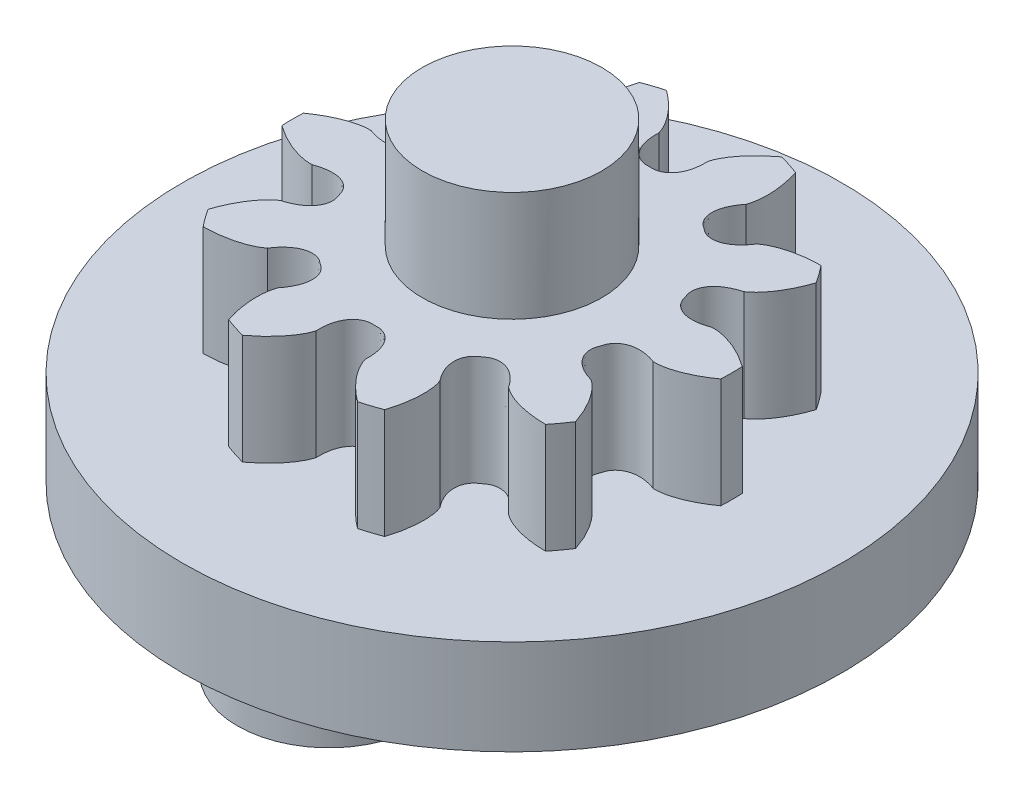
SolidWorks part; units mm, degrees
ref_plane "Front Plane" through (0, 0, 0) normal (0, 0, 1) x (1, 0, 0)
ref_plane "Top Plane" through (0, 0, 0) normal (0, 1, 0) x (1, 0, 0)
ref_plane "Right Plane" through (0, 0, 0) normal (1, 0, 0) x (0, 0, -1)
sketch "Sketch1" plane through (0, 0, 0) normal (0, 1, 0) x (1, 0, 0)
  circle A0 centre (0, 0) radius 9
  dimension "D1" = 18
extrude "Boss-Extrude1" add sketch "Sketch1" along normal blind 2.6
sketch "Sketch2" plane through (0, 0, 0) normal (0, -1, 0) x (1, 0, 0)
  circle A0 centre (-5, 0) radius 2.5
  dimension "D1" = 5
  dimension "D2" = 5
extrude "Boss-Extrude2" add sketch "Sketch2" along normal blind 7
sketch "Sketch3" plane through (0, 2.6, 0) normal (0, 1, 0) x (1, 0, 0)
  arc A0 (-2.1313, -5.6087) -> (-1.5724, -5.7903) centre (0, 0) ccw
  arc A1 (1.5724, -5.7903) -> (2.1313, -5.6087) centre (0, 0) ccw
  arc A2 (4.6756, -3.7602) -> (5.021, -3.2848) centre (0, 0) ccw
  arc A3 (5.9928, -0.2938) -> (5.9928, 0.2938) centre (0, 0) ccw
  arc A4 (5.021, 3.2848) -> (4.6756, 3.7602) centre (0, 0) ccw
  arc A5 (2.1313, 5.6087) -> (1.5724, 5.7903) centre (0, 0) ccw
  arc A6 (-1.5724, 5.7903) -> (-2.1313, 5.6087) centre (0, 0) ccw
  arc A7 (-4.6756, 3.7602) -> (-5.021, 3.2848) centre (0, 0) ccw
  arc A8 (-5.9928, 0.2938) -> (-5.9928, -0.2938) centre (0, 0) ccw
  arc A9 (-5.021, -3.2848) -> (-4.6756, -3.7602) centre (0, 0) ccw
  spline S0 degree 3 poles (-4.6756, -3.7602) (-4.615, -3.759) (-4.4939, -3.7568) (-4.3128, -3.7413) (-4.1328, -3.7163) (-3.9546, -3.6803) (-3.7793, -3.6322) (-3.6366, -3.5809) (-3.5258, -3.532) (-3.4449, -3.4908) (-3.3661, -3.4451) (-3.3178, -3.4086) (-3.2936, -3.3903) knots 0 0 0 0 0.018166 0.036332 0.054498 0.072663 0.090828 0.10899 0.118074 0.127157 0.136239 0.145318 0.145318 0.145318 0.145318 weights 1 1 1 1 1 1 1 1 1 1 1 1 1
  spline S1 degree 3 poles (-3.2936, -3.3903) (-3.2784, -3.3677) (-3.2478, -3.3224) (-3.198, -3.2573) (-3.1447, -3.195) (-3.0866, -3.1371) (-3.0264, -3.0814) (-2.9606, -3.0324) (-2.8916, -2.9881) (-2.8184, -2.9509) (-2.7415, -2.9222) (-2.6617, -2.9026) (-2.58, -2.8939) (-2.4979, -2.8979) (-2.4172, -2.9135) (-2.3532, -2.938) (-2.3043, -2.9625) (-2.2589, -2.993) (-2.2045, -3.0343) (-2.1485, -3.0733) (-2.1054, -3.107) (-2.067, -3.146) (-2.0239, -3.1992) (-1.9842, -3.2712) (-1.955, -3.348) (-1.938, -3.4284) (-1.932, -3.5103) (-1.9355, -3.5923) (-1.9483, -3.6734) (-1.9692, -3.7527) (-1.9954, -3.8305) (-2.0298, -3.9049) (-2.0668, -3.9781) (-2.1096, -4.048) (-2.1561, -4.1156) (-2.1898, -4.1586) (-2.2066, -4.1801) knots 0 0 0 0 0.008194 0.016389 0.024583 0.032776 0.040969 0.049163 0.057354 0.065548 0.073742 0.081932 0.090121 0.098308 0.106495 0.114678 0.118776 0.122873 0.131067 0.139261 0.143358 0.147456 0.155639 0.163826 0.172012 0.180202 0.188392 0.196585 0.204779 0.212971 0.221165 0.229358 0.237551 0.245745 0.253939 0.262134 0.262134 0.262134 0.262134 weights 1 1 1 1 1 1 1 1 1 1 1 1 1 1 1 1 1 1 1 1 1 1 1 1 1 1 1 1 1 1 1 1 1 1 1 1 1
  spline S2 degree 3 poles (-2.2066, -4.1801) (-2.2165, -4.2087) (-2.2363, -4.266) (-2.2554, -4.355) (-2.2696, -4.4447) (-2.2819, -4.5652) (-2.2866, -4.7167) (-2.2781, -4.8983) (-2.2573, -5.0789) (-2.2254, -5.2578) (-2.1842, -5.4349) (-2.1489, -5.5508) (-2.1313, -5.6087) knots 0 0 0 0 0.009079 0.018161 0.027244 0.036327 0.05449 0.072655 0.09082 0.108986 0.127152 0.145318 0.145318 0.145318 0.145318 weights 1 1 1 1 1 1 1 1 1 1 1 1 1
  spline S3 degree 3 poles (-1.5724, -5.7903) (-1.5241, -5.7538) (-1.4275, -5.6808) (-1.2901, -5.5617) (-1.1591, -5.4358) (-1.0361, -5.3018) (-0.9225, -5.1599) (-0.8373, -5.0346) (-0.7763, -4.9299) (-0.7351, -4.8489) (-0.6983, -4.7657) (-0.6806, -4.7078) (-0.6718, -4.6788) knots 0 0 0 0 0.010252 0.020503 0.030755 0.041006 0.051257 0.061507 0.066633 0.071759 0.076884 0.082008 0.082008 0.082008 0.082008 weights 1 1 1 1 1 1 1 1 1 1 1 1 1
  spline S4 degree 3 poles (-0.6718, -4.6788) (-0.6728, -4.6515) (-0.6747, -4.5969) (-0.6727, -4.5149) (-0.6661, -4.4332) (-0.6531, -4.3522) (-0.6372, -4.2718) (-0.6127, -4.1935) (-0.583, -4.117) (-0.5457, -4.0439) (-0.5003, -3.9755) (-0.4473, -3.9128) (-0.3863, -3.8577) (-0.3175, -3.8127) (-0.2431, -3.7778) (-0.1769, -3.7601) (-0.1229, -3.7512) (-0.0683, -3.7492) (0, -3.7505) (0.0683, -3.7492) (0.1229, -3.7512) (0.1769, -3.7601) (0.2431, -3.7778) (0.3175, -3.8127) (0.3863, -3.8577) (0.4473, -3.9128) (0.5003, -3.9755) (0.5457, -4.0439) (0.583, -4.117) (0.6127, -4.1935) (0.6372, -4.2718) (0.6531, -4.3522) (0.6661, -4.4332) (0.6727, -4.5149) (0.6747, -4.5969) (0.6728, -4.6515) (0.6718, -4.6788) knots 0 0 0 0 0.003643 0.007287 0.01093 0.014573 0.018216 0.021859 0.025501 0.029144 0.032787 0.036429 0.04007 0.04371 0.04735 0.050988 0.05281 0.054632 0.058275 0.061918 0.06374 0.065562 0.0692 0.07284 0.07648 0.080121 0.083763 0.087406 0.091049 0.094691 0.098335 0.101977 0.10562 0.109263 0.112907 0.11655 0.11655 0.11655 0.11655 weights 1 1 1 1 1 1 1 1 1 1 1 1 1 1 1 1 1 1 1 1 1 1 1 1 1 1 1 1 1 1 1 1 1 1 1 1 1
  spline S5 degree 3 poles (0.6718, -4.6788) (0.6806, -4.7078) (0.6983, -4.7657) (0.7351, -4.8489) (0.7763, -4.9299) (0.8373, -5.0346) (0.9225, -5.1599) (1.0361, -5.3018) (1.1591, -5.4358) (1.2901, -5.5617) (1.4275, -5.6808) (1.5241, -5.7538) (1.5724, -5.7903) knots 0 0 0 0 0.002373 0.004748 0.007122 0.009497 0.014245 0.018993 0.023742 0.028491 0.03324 0.037989 0.037989 0.037989 0.037989 weights 1 1 1 1 1 1 1 1 1 1 1 1 1
  spline S6 degree 3 poles (2.1313, -5.6087) (2.1489, -5.5508) (2.1842, -5.4349) (2.2254, -5.2578) (2.2573, -5.0789) (2.2781, -4.8983) (2.2866, -4.7167) (2.2819, -4.5652) (2.2696, -4.4447) (2.2554, -4.355) (2.2363, -4.266) (2.2165, -4.2087) (2.2066, -4.1801) knots 0 0 0 0 0.018166 0.036332 0.054498 0.072663 0.090828 0.10899 0.118074 0.127157 0.136239 0.145318 0.145318 0.145318 0.145318 weights 1 1 1 1 1 1 1 1 1 1 1 1 1
  spline S7 degree 3 poles (2.2066, -4.1801) (2.1898, -4.1586) (2.1561, -4.1156) (2.1096, -4.048) (2.0668, -3.9781) (2.0298, -3.9049) (1.9954, -3.8305) (1.9692, -3.7527) (1.9483, -3.6734) (1.9355, -3.5923) (1.932, -3.5103) (1.938, -3.4284) (1.955, -3.348) (1.9842, -3.2712) (2.0239, -3.1992) (2.067, -3.146) (2.1054, -3.107) (2.1485, -3.0733) (2.2045, -3.0343) (2.2589, -2.993) (2.3043, -2.9625) (2.3532, -2.938) (2.4172, -2.9135) (2.4979, -2.8979) (2.58, -2.8939) (2.6617, -2.9026) (2.7415, -2.9222) (2.8184, -2.9509) (2.8916, -2.9881) (2.9606, -3.0324) (3.0264, -3.0814) (3.0866, -3.1371) (3.1447, -3.195) (3.198, -3.2573) (3.2478, -3.3224) (3.2784, -3.3677) (3.2936, -3.3903) knots 0 0 0 0 0.008194 0.016389 0.024583 0.032776 0.040969 0.049163 0.057354 0.065548 0.073742 0.081932 0.090121 0.098308 0.106495 0.114678 0.118776 0.122873 0.131067 0.139261 0.143358 0.147456 0.155639 0.163826 0.172012 0.180202 0.188392 0.196585 0.204779 0.212971 0.221165 0.229358 0.237551 0.245745 0.253939 0.262134 0.262134 0.262134 0.262134 weights 1 1 1 1 1 1 1 1 1 1 1 1 1 1 1 1 1 1 1 1 1 1 1 1 1 1 1 1 1 1 1 1 1 1 1 1 1
  spline S8 degree 3 poles (3.2936, -3.3903) (3.3178, -3.4086) (3.3661, -3.4451) (3.4449, -3.4908) (3.5258, -3.532) (3.6366, -3.5809) (3.7793, -3.6322) (3.9546, -3.6803) (4.1328, -3.7163) (4.3128, -3.7413) (4.4939, -3.7568) (4.615, -3.759) (4.6756, -3.7602) knots 0 0 0 0 0.009079 0.018161 0.027244 0.036327 0.05449 0.072655 0.09082 0.108986 0.127152 0.145318 0.145318 0.145318 0.145318 weights 1 1 1 1 1 1 1 1 1 1 1 1 1
  spline S9 degree 3 poles (5.021, -3.2848) (5.0012, -3.2275) (4.9616, -3.1131) (4.8909, -2.9456) (4.8115, -2.7821) (4.7222, -2.6238) (4.6223, -2.4719) (4.5294, -2.3521) (4.4487, -2.2618) (4.3844, -2.1975) (4.3167, -2.1368) (4.267, -2.1021) (4.2422, -2.0848) knots 0 0 0 0 0.018166 0.036332 0.054498 0.072663 0.090828 0.10899 0.118074 0.127157 0.136239 0.145318 0.145318 0.145318 0.145318 weights 1 1 1 1 1 1 1 1 1 1 1 1 1
  spline S10 degree 3 poles (4.2422, -2.0848) (4.2159, -2.0773) (4.1634, -2.0622) (4.0861, -2.0349) (4.0104, -2.0035) (3.9374, -1.9661) (3.8658, -1.926) (3.7989, -1.8786) (3.7354, -1.8267) (3.6774, -1.7686) (3.6263, -1.7043) (3.5831, -1.6345) (3.5495, -1.5595) (3.528, -1.4802) (3.5178, -1.3986) (3.5214, -1.3302) (3.5296, -1.2761) (3.5446, -1.2235) (3.567, -1.159) (3.5868, -1.0936) (3.6056, -1.0422) (3.6307, -0.9937) (3.668, -0.9363) (3.7242, -0.8762) (3.7883, -0.8247) (3.8595, -0.7837) (3.9355, -0.7527) (4.0146, -0.7307) (4.0957, -0.7178) (4.1776, -0.7131) (4.2596, -0.7141) (4.3411, -0.7238) (4.422, -0.7364) (4.5018, -0.7555) (4.5804, -0.7788) (4.6317, -0.7975) (4.6574, -0.8069) knots 0 0 0 0 0.008194 0.016389 0.024583 0.032776 0.040969 0.049163 0.057354 0.065548 0.073742 0.081932 0.090121 0.098308 0.106495 0.114678 0.118776 0.122873 0.131067 0.139261 0.143358 0.147456 0.155639 0.163826 0.172012 0.180202 0.188392 0.196585 0.204779 0.212971 0.221165 0.229358 0.237551 0.245745 0.253939 0.262134 0.262134 0.262134 0.262134 weights 1 1 1 1 1 1 1 1 1 1 1 1 1 1 1 1 1 1 1 1 1 1 1 1 1 1 1 1 1 1 1 1 1 1 1 1 1
  spline S11 degree 3 poles (4.6574, -0.8069) (4.6877, -0.8075) (4.7483, -0.8086) (4.8388, -0.7993) (4.9285, -0.7851) (5.0469, -0.7595) (5.1925, -0.7171) (5.3625, -0.6529) (5.5279, -0.5774) (5.6882, -0.4918) (5.8438, -0.3978) (5.9431, -0.3285) (5.9928, -0.2938) knots 0 0 0 0 0.009079 0.018161 0.027244 0.036327 0.05449 0.072655 0.09082 0.108986 0.127152 0.145318 0.145318 0.145318 0.145318 weights 1 1 1 1 1 1 1 1 1 1 1 1 1
  spline S12 degree 3 poles (5.9928, 0.2938) (5.9431, 0.3285) (5.8438, 0.3978) (5.6882, 0.4918) (5.5279, 0.5774) (5.3625, 0.6529) (5.1925, 0.7171) (5.0469, 0.7595) (4.9285, 0.7851) (4.8388, 0.7993) (4.7483, 0.8086) (4.6877, 0.8075) (4.6574, 0.8069) knots 0 0 0 0 0.018166 0.036332 0.054498 0.072663 0.090828 0.10899 0.118074 0.127157 0.136239 0.145318 0.145318 0.145318 0.145318 weights 1 1 1 1 1 1 1 1 1 1 1 1 1
  spline S13 degree 3 poles (4.6574, 0.8069) (4.6317, 0.7975) (4.5804, 0.7788) (4.5018, 0.7555) (4.422, 0.7364) (4.3411, 0.7238) (4.2596, 0.7141) (4.1776, 0.7131) (4.0957, 0.7178) (4.0146, 0.7307) (3.9355, 0.7527) (3.8595, 0.7837) (3.7883, 0.8247) (3.7242, 0.8762) (3.668, 0.9363) (3.6307, 0.9937) (3.6056, 1.0422) (3.5868, 1.0936) (3.567, 1.159) (3.5446, 1.2235) (3.5296, 1.2761) (3.5214, 1.3302) (3.5178, 1.3986) (3.528, 1.4802) (3.5495, 1.5595) (3.5831, 1.6345) (3.6263, 1.7043) (3.6774, 1.7686) (3.7354, 1.8267) (3.7989, 1.8786) (3.8658, 1.926) (3.9374, 1.9661) (4.0104, 2.0035) (4.0861, 2.0349) (4.1634, 2.0622) (4.2159, 2.0773) (4.2422, 2.0848) knots 0 0 0 0 0.008194 0.016389 0.024583 0.032776 0.040969 0.049163 0.057354 0.065548 0.073742 0.081932 0.090121 0.098308 0.106495 0.114678 0.118776 0.122873 0.131067 0.139261 0.143358 0.147456 0.155639 0.163826 0.172012 0.180202 0.188392 0.196585 0.204779 0.212971 0.221165 0.229358 0.237551 0.245745 0.253939 0.262134 0.262134 0.262134 0.262134 weights 1 1 1 1 1 1 1 1 1 1 1 1 1 1 1 1 1 1 1 1 1 1 1 1 1 1 1 1 1 1 1 1 1 1 1 1 1
  spline S14 degree 3 poles (4.2422, 2.0848) (4.267, 2.1021) (4.3167, 2.1368) (4.3844, 2.1975) (4.4487, 2.2618) (4.5294, 2.3521) (4.6223, 2.4719) (4.7222, 2.6238) (4.8115, 2.7821) (4.8909, 2.9456) (4.9616, 3.1131) (5.0012, 3.2275) (5.021, 3.2848) knots 0 0 0 0 0.009079 0.018161 0.027244 0.036327 0.05449 0.072655 0.09082 0.108986 0.127152 0.145318 0.145318 0.145318 0.145318 weights 1 1 1 1 1 1 1 1 1 1 1 1 1
  spline S15 degree 3 poles (4.6756, 3.7602) (4.615, 3.759) (4.4939, 3.7568) (4.3128, 3.7413) (4.1328, 3.7163) (3.9546, 3.6803) (3.7793, 3.6322) (3.6366, 3.5809) (3.5258, 3.532) (3.4449, 3.4908) (3.3661, 3.4451) (3.3178, 3.4086) (3.2936, 3.3903) knots 0 0 0 0 0.018166 0.036332 0.054498 0.072663 0.090828 0.10899 0.118074 0.127157 0.136239 0.145318 0.145318 0.145318 0.145318 weights 1 1 1 1 1 1 1 1 1 1 1 1 1
  spline S16 degree 3 poles (3.2936, 3.3903) (3.2784, 3.3677) (3.2478, 3.3224) (3.198, 3.2573) (3.1447, 3.195) (3.0866, 3.1371) (3.0264, 3.0814) (2.9606, 3.0324) (2.8916, 2.9881) (2.8184, 2.9509) (2.7415, 2.9222) (2.6617, 2.9026) (2.58, 2.8939) (2.4979, 2.8979) (2.4172, 2.9135) (2.3532, 2.938) (2.3043, 2.9625) (2.2589, 2.993) (2.2045, 3.0343) (2.1485, 3.0733) (2.1054, 3.107) (2.067, 3.146) (2.0239, 3.1992) (1.9842, 3.2712) (1.955, 3.348) (1.938, 3.4284) (1.932, 3.5103) (1.9355, 3.5923) (1.9483, 3.6734) (1.9692, 3.7527) (1.9954, 3.8305) (2.0298, 3.9049) (2.0668, 3.9781) (2.1096, 4.048) (2.1561, 4.1156) (2.1898, 4.1586) (2.2066, 4.1801) knots 0 0 0 0 0.008194 0.016389 0.024583 0.032776 0.040969 0.049163 0.057354 0.065548 0.073742 0.081932 0.090121 0.098308 0.106495 0.114678 0.118776 0.122873 0.131067 0.139261 0.143358 0.147456 0.155639 0.163826 0.172012 0.180202 0.188392 0.196585 0.204779 0.212971 0.221165 0.229358 0.237551 0.245745 0.253939 0.262134 0.262134 0.262134 0.262134 weights 1 1 1 1 1 1 1 1 1 1 1 1 1 1 1 1 1 1 1 1 1 1 1 1 1 1 1 1 1 1 1 1 1 1 1 1 1
  spline S17 degree 3 poles (2.2066, 4.1801) (2.2165, 4.2087) (2.2363, 4.266) (2.2554, 4.355) (2.2696, 4.4447) (2.2819, 4.5652) (2.2866, 4.7167) (2.2781, 4.8983) (2.2573, 5.0789) (2.2254, 5.2578) (2.1842, 5.4349) (2.1489, 5.5508) (2.1313, 5.6087) knots 0 0 0 0 0.009079 0.018161 0.027244 0.036327 0.05449 0.072655 0.09082 0.108986 0.127152 0.145318 0.145318 0.145318 0.145318 weights 1 1 1 1 1 1 1 1 1 1 1 1 1
  spline S18 degree 3 poles (1.5724, 5.7903) (1.5241, 5.7538) (1.4275, 5.6808) (1.2901, 5.5617) (1.1591, 5.4358) (1.0361, 5.3018) (0.9225, 5.1599) (0.8373, 5.0346) (0.7763, 4.9299) (0.7351, 4.8489) (0.6983, 4.7657) (0.6806, 4.7078) (0.6718, 4.6788) knots 0 0 0 0 0.018166 0.036332 0.054498 0.072663 0.090828 0.10899 0.118074 0.127157 0.136239 0.145318 0.145318 0.145318 0.145318 weights 1 1 1 1 1 1 1 1 1 1 1 1 1
  spline S19 degree 3 poles (0.6718, 4.6788) (0.6728, 4.6515) (0.6747, 4.5969) (0.6727, 4.5149) (0.6661, 4.4332) (0.6531, 4.3522) (0.6372, 4.2718) (0.6127, 4.1935) (0.583, 4.117) (0.5457, 4.0439) (0.5003, 3.9755) (0.4473, 3.9128) (0.3863, 3.8577) (0.3175, 3.8127) (0.2431, 3.7778) (0.1769, 3.7601) (0.1229, 3.7512) (0.0683, 3.7492) (0, 3.7505) (-0.0683, 3.7492) (-0.1229, 3.7512) (-0.1769, 3.7601) (-0.2431, 3.7778) (-0.3175, 3.8127) (-0.3863, 3.8577) (-0.4473, 3.9128) (-0.5003, 3.9755) (-0.5457, 4.0439) (-0.583, 4.117) (-0.6127, 4.1935) (-0.6372, 4.2718) (-0.6531, 4.3522) (-0.6661, 4.4332) (-0.6727, 4.5149) (-0.6747, 4.5969) (-0.6728, 4.6515) (-0.6718, 4.6788) knots 0 0 0 0 0.008194 0.016389 0.024583 0.032776 0.040969 0.049163 0.057354 0.065548 0.073742 0.081932 0.090121 0.098308 0.106495 0.114678 0.118776 0.122873 0.131067 0.139261 0.143358 0.147456 0.155639 0.163826 0.172012 0.180202 0.188392 0.196585 0.204779 0.212971 0.221165 0.229358 0.237551 0.245745 0.253939 0.262134 0.262134 0.262134 0.262134 weights 1 1 1 1 1 1 1 1 1 1 1 1 1 1 1 1 1 1 1 1 1 1 1 1 1 1 1 1 1 1 1 1 1 1 1 1 1
  spline S20 degree 3 poles (-0.6718, 4.6788) (-0.6806, 4.7078) (-0.6983, 4.7657) (-0.7351, 4.8489) (-0.7763, 4.9299) (-0.8373, 5.0346) (-0.9225, 5.1599) (-1.0361, 5.3018) (-1.1591, 5.4358) (-1.2901, 5.5617) (-1.4275, 5.6808) (-1.5241, 5.7538) (-1.5724, 5.7903) knots 0 0 0 0 0.009079 0.018161 0.027244 0.036327 0.05449 0.072655 0.09082 0.108986 0.127152 0.145318 0.145318 0.145318 0.145318 weights 1 1 1 1 1 1 1 1 1 1 1 1 1
  spline S21 degree 3 poles (-2.1313, 5.6087) (-2.1489, 5.5508) (-2.1842, 5.4349) (-2.2254, 5.2578) (-2.2573, 5.0789) (-2.2781, 4.8983) (-2.2866, 4.7167) (-2.2819, 4.5652) (-2.2696, 4.4447) (-2.2554, 4.355) (-2.2363, 4.266) (-2.2165, 4.2087) (-2.2066, 4.1801) knots 0 0 0 0 0.018166 0.036332 0.054498 0.072663 0.090828 0.10899 0.118074 0.127157 0.136239 0.145318 0.145318 0.145318 0.145318 weights 1 1 1 1 1 1 1 1 1 1 1 1 1
  spline S22 degree 3 poles (-2.2066, 4.1801) (-2.1898, 4.1586) (-2.1561, 4.1156) (-2.1096, 4.048) (-2.0668, 3.9781) (-2.0298, 3.9049) (-1.9954, 3.8305) (-1.9692, 3.7527) (-1.9483, 3.6734) (-1.9355, 3.5923) (-1.932, 3.5103) (-1.938, 3.4284) (-1.955, 3.348) (-1.9842, 3.2712) (-2.0239, 3.1992) (-2.067, 3.146) (-2.1054, 3.107) (-2.1485, 3.0733) (-2.2045, 3.0343) (-2.2589, 2.993) (-2.3043, 2.9625) (-2.3532, 2.938) (-2.4172, 2.9135) (-2.4979, 2.8979) (-2.58, 2.8939) (-2.6617, 2.9026) (-2.7415, 2.9222) (-2.8184, 2.9509) (-2.8916, 2.9881) (-2.9606, 3.0324) (-3.0264, 3.0814) (-3.0866, 3.1371) (-3.1447, 3.195) (-3.198, 3.2573) (-3.2478, 3.3224) (-3.2784, 3.3677) (-3.2936, 3.3903) knots 0 0 0 0 0.008194 0.016389 0.024583 0.032776 0.040969 0.049163 0.057354 0.065548 0.073742 0.081932 0.090121 0.098308 0.106495 0.114678 0.118776 0.122873 0.131067 0.139261 0.143358 0.147456 0.155639 0.163826 0.172012 0.180202 0.188392 0.196585 0.204779 0.212971 0.221165 0.229358 0.237551 0.245745 0.253939 0.262134 0.262134 0.262134 0.262134 weights 1 1 1 1 1 1 1 1 1 1 1 1 1 1 1 1 1 1 1 1 1 1 1 1 1 1 1 1 1 1 1 1 1 1 1 1 1
  spline S23 degree 3 poles (-3.2936, 3.3903) (-3.3178, 3.4086) (-3.3661, 3.4451) (-3.4449, 3.4908) (-3.5258, 3.532) (-3.6366, 3.5809) (-3.7793, 3.6322) (-3.9546, 3.6803) (-4.1328, 3.7163) (-4.3128, 3.7413) (-4.4939, 3.7568) (-4.615, 3.759) (-4.6756, 3.7602) knots 0 0 0 0 0.009079 0.018161 0.027244 0.036327 0.05449 0.072655 0.09082 0.108986 0.127152 0.145318 0.145318 0.145318 0.145318 weights 1 1 1 1 1 1 1 1 1 1 1 1 1
  spline S24 degree 3 poles (-5.021, 3.2848) (-5.0012, 3.2275) (-4.9616, 3.1131) (-4.8909, 2.9456) (-4.8115, 2.7821) (-4.7222, 2.6238) (-4.6223, 2.4719) (-4.5294, 2.3521) (-4.4487, 2.2618) (-4.3844, 2.1975) (-4.3167, 2.1368) (-4.267, 2.1021) (-4.2422, 2.0848) knots 0 0 0 0 0.018166 0.036332 0.054498 0.072663 0.090828 0.10899 0.118074 0.127157 0.136239 0.145318 0.145318 0.145318 0.145318 weights 1 1 1 1 1 1 1 1 1 1 1 1 1
  spline S25 degree 3 poles (-4.2422, 2.0848) (-4.2159, 2.0773) (-4.1634, 2.0622) (-4.0861, 2.0349) (-4.0104, 2.0035) (-3.9374, 1.9661) (-3.8658, 1.926) (-3.7989, 1.8786) (-3.7354, 1.8267) (-3.6774, 1.7686) (-3.6263, 1.7043) (-3.5831, 1.6345) (-3.5495, 1.5595) (-3.528, 1.4802) (-3.5178, 1.3986) (-3.5214, 1.3302) (-3.5296, 1.2761) (-3.5446, 1.2235) (-3.567, 1.159) (-3.5868, 1.0936) (-3.6056, 1.0422) (-3.6307, 0.9937) (-3.668, 0.9363) (-3.7242, 0.8762) (-3.7883, 0.8247) (-3.8595, 0.7837) (-3.9355, 0.7527) (-4.0146, 0.7307) (-4.0957, 0.7178) (-4.1776, 0.7131) (-4.2596, 0.7141) (-4.3411, 0.7238) (-4.422, 0.7364) (-4.5018, 0.7555) (-4.5804, 0.7788) (-4.6317, 0.7975) (-4.6574, 0.8069) knots 0 0 0 0 0.008194 0.016389 0.024583 0.032776 0.040969 0.049163 0.057354 0.065548 0.073742 0.081932 0.090121 0.098308 0.106495 0.114678 0.118776 0.122873 0.131067 0.139261 0.143358 0.147456 0.155639 0.163826 0.172012 0.180202 0.188392 0.196585 0.204779 0.212971 0.221165 0.229358 0.237551 0.245745 0.253939 0.262134 0.262134 0.262134 0.262134 weights 1 1 1 1 1 1 1 1 1 1 1 1 1 1 1 1 1 1 1 1 1 1 1 1 1 1 1 1 1 1 1 1 1 1 1 1 1
  spline S26 degree 3 poles (-4.6574, 0.8069) (-4.6877, 0.8075) (-4.7483, 0.8086) (-4.8388, 0.7993) (-4.9285, 0.7851) (-5.0469, 0.7595) (-5.1925, 0.7171) (-5.3625, 0.6529) (-5.5279, 0.5774) (-5.6882, 0.4918) (-5.8438, 0.3978) (-5.9431, 0.3285) (-5.9928, 0.2938) knots 0 0 0 0 0.009079 0.018161 0.027244 0.036327 0.05449 0.072655 0.09082 0.108986 0.127152 0.145318 0.145318 0.145318 0.145318 weights 1 1 1 1 1 1 1 1 1 1 1 1 1
  spline S27 degree 3 poles (-5.9928, -0.2938) (-5.9431, -0.3285) (-5.8438, -0.3978) (-5.6882, -0.4918) (-5.5279, -0.5774) (-5.3625, -0.6529) (-5.1925, -0.7171) (-5.0469, -0.7595) (-4.9285, -0.7851) (-4.8388, -0.7993) (-4.7483, -0.8086) (-4.6877, -0.8075) (-4.6574, -0.8069) knots 0 0 0 0 0.018166 0.036332 0.054498 0.072663 0.090828 0.10899 0.118074 0.127157 0.136239 0.145318 0.145318 0.145318 0.145318 weights 1 1 1 1 1 1 1 1 1 1 1 1 1
  spline S28 degree 3 poles (-4.6574, -0.8069) (-4.6317, -0.7975) (-4.5804, -0.7788) (-4.5018, -0.7555) (-4.422, -0.7364) (-4.3411, -0.7238) (-4.2596, -0.7141) (-4.1776, -0.7131) (-4.0957, -0.7178) (-4.0146, -0.7307) (-3.9355, -0.7527) (-3.8595, -0.7837) (-3.7883, -0.8247) (-3.7242, -0.8762) (-3.668, -0.9363) (-3.6307, -0.9937) (-3.6056, -1.0422) (-3.5868, -1.0936) (-3.567, -1.159) (-3.5446, -1.2235) (-3.5296, -1.2761) (-3.5214, -1.3302) (-3.5178, -1.3986) (-3.528, -1.4802) (-3.5495, -1.5595) (-3.5831, -1.6345) (-3.6263, -1.7043) (-3.6774, -1.7686) (-3.7354, -1.8267) (-3.7989, -1.8786) (-3.8658, -1.926) (-3.9374, -1.9661) (-4.0104, -2.0035) (-4.0861, -2.0349) (-4.1634, -2.0622) (-4.2159, -2.0773) (-4.2422, -2.0848) knots 0 0 0 0 0.008194 0.016389 0.024583 0.032776 0.040969 0.049163 0.057354 0.065548 0.073742 0.081932 0.090121 0.098308 0.106495 0.114678 0.118776 0.122873 0.131067 0.139261 0.143358 0.147456 0.155639 0.163826 0.172012 0.180202 0.188392 0.196585 0.204779 0.212971 0.221165 0.229358 0.237551 0.245745 0.253939 0.262134 0.262134 0.262134 0.262134 weights 1 1 1 1 1 1 1 1 1 1 1 1 1 1 1 1 1 1 1 1 1 1 1 1 1 1 1 1 1 1 1 1 1 1 1 1 1
  spline S29 degree 3 poles (-4.2422, -2.0848) (-4.267, -2.1021) (-4.3167, -2.1368) (-4.3844, -2.1975) (-4.4487, -2.2618) (-4.5294, -2.3521) (-4.6223, -2.4719) (-4.7222, -2.6238) (-4.8115, -2.7821) (-4.8909, -2.9456) (-4.9616, -3.1131) (-5.0012, -3.2275) (-5.021, -3.2848) knots 0 0 0 0 0.009079 0.018161 0.027244 0.036327 0.05449 0.072655 0.09082 0.108986 0.127152 0.145318 0.145318 0.145318 0.145318 weights 1 1 1 1 1 1 1 1 1 1 1 1 1
extrude "Boss-Extrude3" add sketch "Sketch3" along normal blind 3
sketch "Sketch4" plane through (0, 5.6, 0) normal (0, 1, 0) x (1, 0, 0)
  circle A0 centre (0, 0) radius 2.45
  dimension "D1" = 4.9
extrude "Boss-Extrude4" add sketch "Sketch4" along normal blind 3
